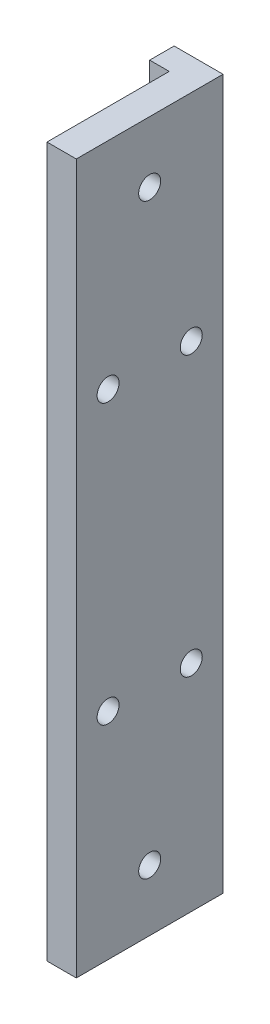
SolidWorks part; units mm, degrees
ref_plane "Front Plane" through (0, 0, 0) normal (0, 0, 1) x (1, 0, 0)
ref_plane "Top Plane" through (0, 0, 0) normal (0, 1, 0) x (1, 0, 0)
ref_plane "Right Plane" through (0, 0, 0) normal (1, 0, 0) x (0, 0, -1)
ref_plane "Plane1" through (0, 260, 0) normal (0, -1, 0) x (-1, 0, 0)
sketch "Sketch1" plane through (0, 260, 0) normal (0, -1, 0) x (-1, 0, 0)
  line L0 (71.5, -127.5) -> (61.5, -127.5)
  line L1 (61.5, -127.5) -> (61.5, -97.5)
  line L2 (61.5, -97.5) -> (71.5, -97.5)
  line L3 (71.5, -97.5) -> (71.5, -102.5)
  line L4 (71.5, -102.5) -> (67.5, -102.5)
  line L5 (67.5, -102.5) -> (67.5, -122.5)
  line L6 (67.5, -122.5) -> (71.5, -122.5)
  line L7 (71.5, -122.5) -> (71.5, -127.5)
  line L8 (68.9986, -122.5) -> (74.3631, -122.5) construction
  line L9 (68.9986, -102.5) -> (74.3631, -102.5) construction
  line L10 (67.5, -115.6369) -> (67.5, -121.0014) construction
  dimension "D1" = 5
  dimension "D2" = 10
  dimension "D3" = 6
extrude "Boss-Extrude1" add sketch "Sketch1" along normal blind 145
sketch "Sketch5" plane through (-61.5, 0, 0) normal (1, 0, 0) x (0, 0, -1)
  line L0 (-97.5, 260) -> (-127.5, 260) construction
  line L1 (-121, 159) -> (-104, 159) construction
  line L2 (-121, 159) -> (-121, 216) construction
  line L3 (-121, 216) -> (-104, 216) construction
  line L4 (-104, 159) -> (-104, 216) construction
  line L5 (-121, 159) -> (-104, 216) construction
  line L6 (-121, 216) -> (-104, 159) construction
  line L7 (-97.5, 115) -> (-97.5, 260) construction
  point P0 (-112.5, 187.5)
  point P8 (-112.5, 260)
  point P11 (-97.5, 187.5)
  dimension "D1" = 17
  dimension "D2" = 57
hole_wizard "M4 Clearance Hole1" positions "Sketch2" profile "Sketch4" hole size "M4" standard "ISO" end condition through all
sketch "Sketch2" plane through (-61.5, 0, 0) normal (1, 0, 0) x (0, 0, -1)
  line L0 (-112.5, 247.5) -> (-112.5, 127.5) construction
  line L2 (-97.5, 260) -> (-127.5, 260) construction
  line L4 (-112.5, 247.5) -> (-112.5, 260) construction
  line L7 (-112.5, 127.5) -> (-112.5, 115) construction
  line L8 (-97.5, 115) -> (-127.5, 115) construction
  point P1 (-112.5, 247.5)
  point P2 (-112.5, 127.5)
  point P7 (-112.5, 260)
  dimension "D1" = 120
sketch "Sketch4" plane through (-61.5, 247.5, 112.5) normal (0, 1, 0) x (0, 0, -1)
  line L0 (0, 0) -> (0, 10)
  line L1 (0, 10) -> (2.25, 10)
  line L2 (2.25, 10) -> (2.25, 0)
  line L5 (2.25, 0) -> (0, 0)
  line L11 (0, -6.35) -> (0, 107.95) construction
  dimension "Thru Hole Dia." = 4.5
  dimension "Thru Hole Depth" = 10
hole_wizard "Hole1" positions "Sketch6" profile "Sketch7" legacy
sketch "Sketch6" plane through (-61.5, 0, 0) normal (1, 0, 0) x (0, 0, -1)
  point P0 (-104, 216)
  point P3 (-121, 216)
  point P6 (-104, 159)
  point P9 (-121, 159)
sketch "Sketch7" plane through (-61.5, 216, 104) normal (0, 1, 0) x (0, 0, -1)
  line L0 (0, 0) -> (0, 6)
  line L1 (0, 6) -> (2.25, 6)
  line L2 (2.25, 6) -> (2.25, 0)
  line L3 (2.25, 0) -> (0, 0)
  line L4 (0, 110) -> (0, -10) construction
  dimension "Diameter" = 4.5
  dimension "Depth" = 6
sketch "Sketch8" plane through (-71.5, 0, 0) normal (-1, 0, 0) x (0, 0, 1)
  line L4 (127.5, 260) -> (122.5, 260)
  line L5 (122.5, 260) -> (122.5, 115)
  line L6 (122.5, 115) -> (127.5, 115)
  line L7 (127.5, 115) -> (127.5, 260)
  line L8 (127.5, 260) -> (122.5, 260)
  line L9 (122.5, 260) -> (122.5, 115)
  line L10 (122.5, 115) -> (127.5, 115)
  line L11 (127.5, 115) -> (127.5, 260)
  dimension "D1" = 0
extrude "Cut-Extrude1" cut sketch "Sketch8" against normal up to surface (4 mm away) up to face at (-67.5, 247.5, 110.25)
